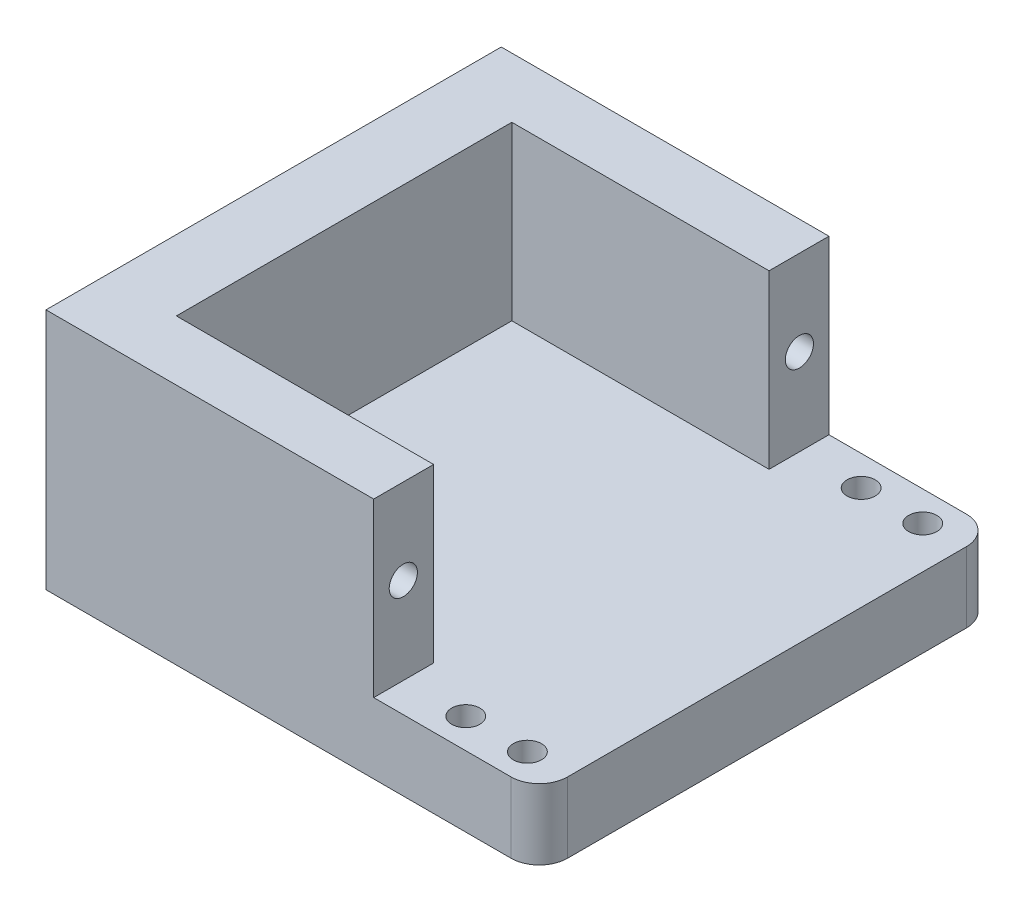
SolidWorks part; units mm, degrees
ref_plane "Front Plane" through (0, 0, 0) normal (0, 0, 1) x (1, 0, 0)
ref_plane "Top Plane" through (0, 0, 0) normal (0, 1, 0) x (1, 0, 0)
ref_plane "Right Plane" through (0, 0, 0) normal (1, 0, 0) x (0, 0, -1)
sketch "Sketch4" plane through (0, 0, 0) normal (0, 1, 0) x (1, 0, 0)
  line L1 (0, 0) -> (35, 0)
  line L2 (0, 0) -> (0, 32.3)
  line L3 (0, 32.3) -> (35, 32.3)
  line L4 (35, 0) -> (35, 32.3)
  dimension "D1" = 35
  dimension "D2" = 32.3
extrude "Boss-Extrude3" add sketch "Sketch4" along normal blind 5
sketch "Sketch6" plane through (0, 5, 0) normal (0, 1, 0) x (1, 0, 0)
  line L0 (5, 32.3) -> (5, 0)
  line L1 (35, 32.3) -> (0, 32.3) construction
  line L2 (0, 0) -> (35, 0) construction
  line L3 (5, 0) -> (0, 0)
  line L4 (0, 0) -> (0, 32.3)
  line L5 (0, 32.3) -> (5, 32.3)
  dimension "D1" = 5
extrude "Boss-Extrude5" add sketch "Sketch6" along normal blind 12.2
sketch "Sketch7" plane through (0, 5, 0) normal (0, 1, 0) x (1, 0, 0)
  line L1 (35, 32.3) -> (5, 32.3) construction
  line L6 (5, 32.3) -> (5, 0)
  line L7 (5, 0) -> (35, 0)
  line L8 (35, 0) -> (35, 32.3)
  line L9 (35, 32.3) -> (5, 32.3)
  line L13 (23.25, 32.3) -> (5, 32.3)
  dimension "D1" = 18.25
  dimension "D2" = 0
sketch "Sketch8" plane through (0, 5, 0) normal (0, 1, 0) x (1, 0, 0)
  line L0 (23.25, 32.3) -> (23.25, 28.05)
  line L1 (23.25, 28.05) -> (5, 28.05)
  line L2 (5, 0) -> (5, 32.3) construction
  line L3 (5, 28.05) -> (5, 32.3)
  line L4 (5, 32.3) -> (23.25, 32.3)
  line L5 (35, 16.15) -> (5, 16.15)
  line L6 (35, 0) -> (35, 32.3) construction
  line L7 (5, 4.25) -> (5, 0)
  line L8 (23.25, 4.25) -> (5, 4.25)
  line L9 (23.25, 0) -> (23.25, 4.25)
  line L10 (5, 0) -> (23.25, 0)
  line M5 (5, 32.3) -> (5, 0)
  line M6 (5, 0) -> (35, 0)
  line M8 (35, 32.3) -> (5, 32.3)
  dimension "D1" = 4.25
extrude "Boss-Extrude6" add sketch "Sketch8" along normal blind 12.2 contours L9 L8 M6 M5 | L1 L0 M8 M5
sketch "Sketch9" plane through (23.25, 0, 0) normal (1, 0, 0) x (0, 0, -1)
  line L0 (0, 5) -> (0, 10.5)
  line L1 (0, 17.2) -> (0, 5) construction
  line L2 (0, 10.5) -> (1.35, 10.5)
  dimension "D1" = 5.5
  dimension "D2" = 1.35
sketch "Sketch10" plane through (23.25, 0, 0) normal (1, 0, 0) x (0, 0, -1)
  line L1 (0, 17.2) -> (0, 5) construction
  line L2 (16.15, 17.2) -> (16.15, 5)
  line L3 (4.25, 17.2) -> (28.05, 17.2) construction
  line L4 (0, 5) -> (32.3, 5) construction
  circle A0 centre (2.1, 11.15) radius 1
  circle A1 centre (30.2, 11.15) radius 1
  dimension "D1" = 2
  dimension "D2" = 0.65
  dimension "D3" = 2.1
extrude "Cut-Extrude1" cut sketch "Sketch10" against normal blind 5 contours A0 | A1
sketch "Sketch11" plane through (0, 5, 0) normal (0, 1, 0) x (1, 0, 0)
  line L0 (23.25, 30.175) -> (35, 30.175)
  line L1 (23.25, 32.3) -> (23.25, 28.05) construction
  line L2 (35, 0) -> (35, 32.3) construction
  line L3 (35, 16.15) -> (5, 16.15)
  line L4 (5, 4.25) -> (5, 28.05) construction
  circle A0 centre (32.0281, 30.175) radius 1
  circle A1 centre (27.6571, 30.175) radius 1
  circle A2 centre (32.0281, 2.125) radius 1
  circle A3 centre (27.6571, 2.125) radius 1
  dimension "D1" = 2
  dimension "D2" = 2
extrude "Cut-Extrude2" cut sketch "Sketch11" against normal blind 5 contours L0 A1 | L0 A1 | L0 A0 | L0 A0 | A3 | A2
sketch "Sketch12" plane through (0, 0, 0) normal (0, -1, 0) x (1, 0, 0)
  line L0 (0, -16.15) -> (35, -16.15)
  line L1 (0, -32.3) -> (0, 0) construction
  line L2 (35, 0) -> (35, -32.3) construction
  circle A1 centre (2.3223, -2.125) radius 1
  circle A2 centre (2.3223, -30.175) radius 1
  dimension "D1" = 2
extrude "Cut-Extrude3" cut sketch "Sketch12" against normal blind 5 contours A1 | A2
fillet "Fillet2" radius 2 2 edges at (35, 2.5, -32.3) (35, 2.5, 0)
